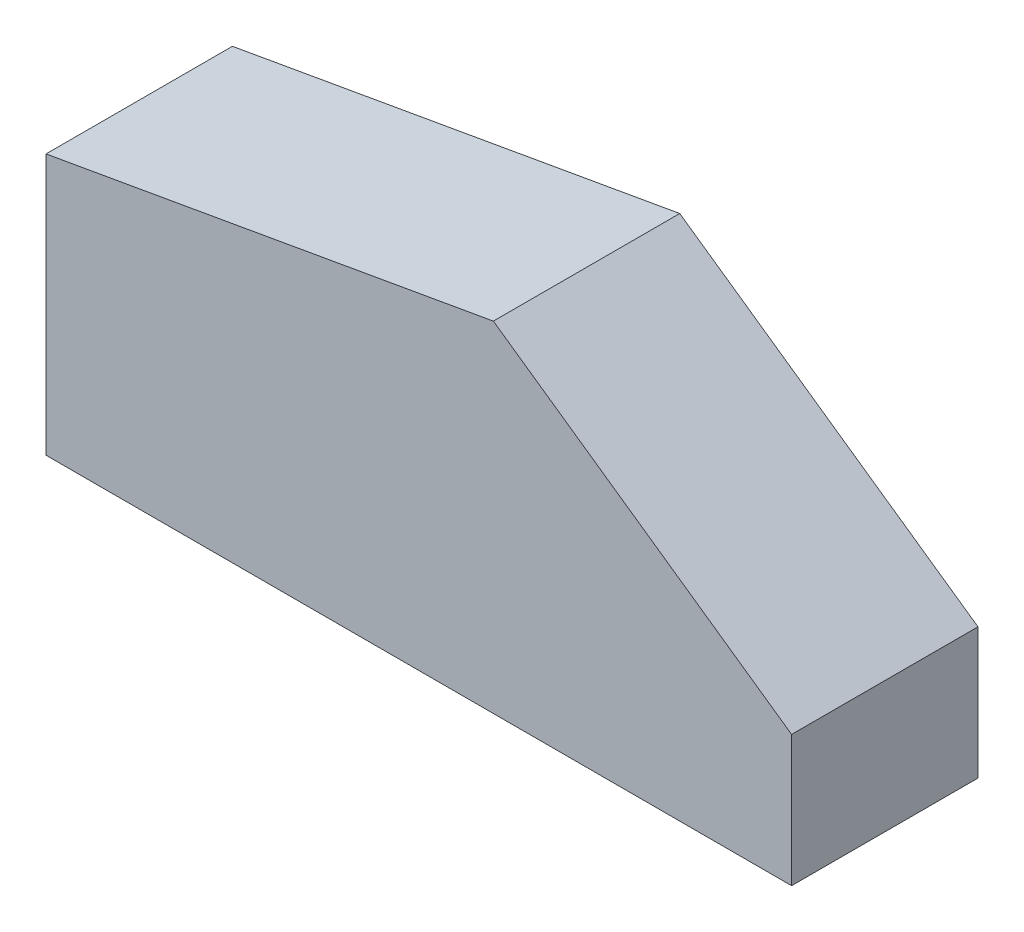
SolidWorks part; units mm, degrees
ref_plane "Front Plane" through (0, 0, 0) normal (0, 0, 1) x (1, 0, 0)
ref_plane "Top Plane" through (0, 0, 0) normal (0, 1, 0) x (1, 0, 0)
ref_plane "Right Plane" through (0, 0, 0) normal (1, 0, 0) x (0, 0, -1)
sketch "Sketch1" plane through (0, 0, 0) normal (0, 0, 1) x (1, 0, 0)
  line L0 (0, 0) -> (0, 35)
  line L1 (0, 35) -> (60, 45.5796)
  line L2 (60, 45.5796) -> (100, 17.5713)
  line L3 (100, 17.5713) -> (100, 0)
  line L4 (100, 0) -> (0, 0)
  dimension "D1" = 35
  dimension "D2" = 100
  dimension "D3" = 60
  dimension "D4" = 135
  dimension "D5" = 100
extrude "Boss-Extrude1" add sketch "Sketch1" along normal blind 25
